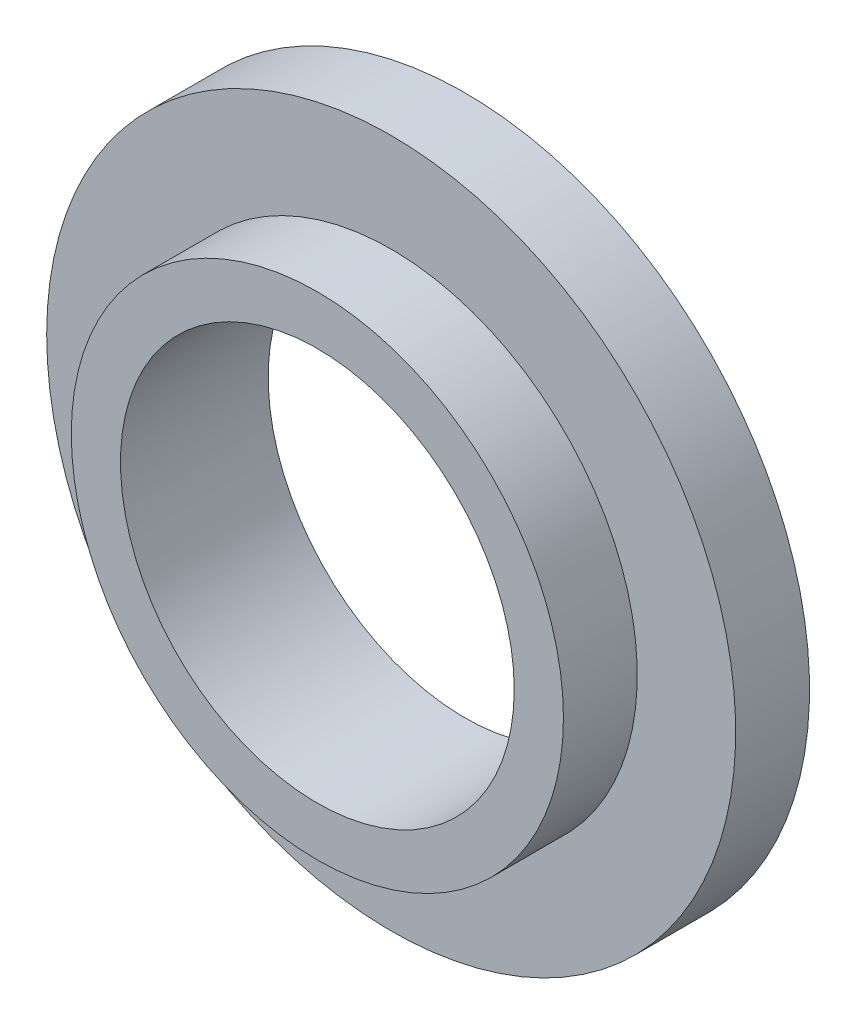
SolidWorks part; units mm, degrees
ref_plane "Front Plane" through (0, 0, 0) normal (0, 0, 1) x (1, 0, 0)
ref_plane "Top Plane" through (0, 0, 0) normal (0, 1, 0) x (1, 0, 0)
ref_plane "Right Plane" through (0, 0, 0) normal (1, 0, 0) x (0, 0, -1)
sketch "Sketch1" plane through (0, 0, 0) normal (0, 0, 1) x (1, 0, 0)
  circle A0 centre (0, 0) radius 20
  circle A1 centre (0, 0) radius 25
  dimension "D1" = 40
  dimension "D2" = 50
extrude "Boss-Extrude1" add sketch "Sketch1" along normal blind 15
sketch "Sketch2" plane through (0, 0, 0) normal (0, 0, -1) x (-1, 0, 0)
  circle A0 centre (0, 0) radius 35
  circle M1 centre (0, 0) radius 25
  dimension "D1" = 70
extrude "Boss-Extrude2" add sketch "Sketch2" against normal blind 7.5 contours A0 M1
